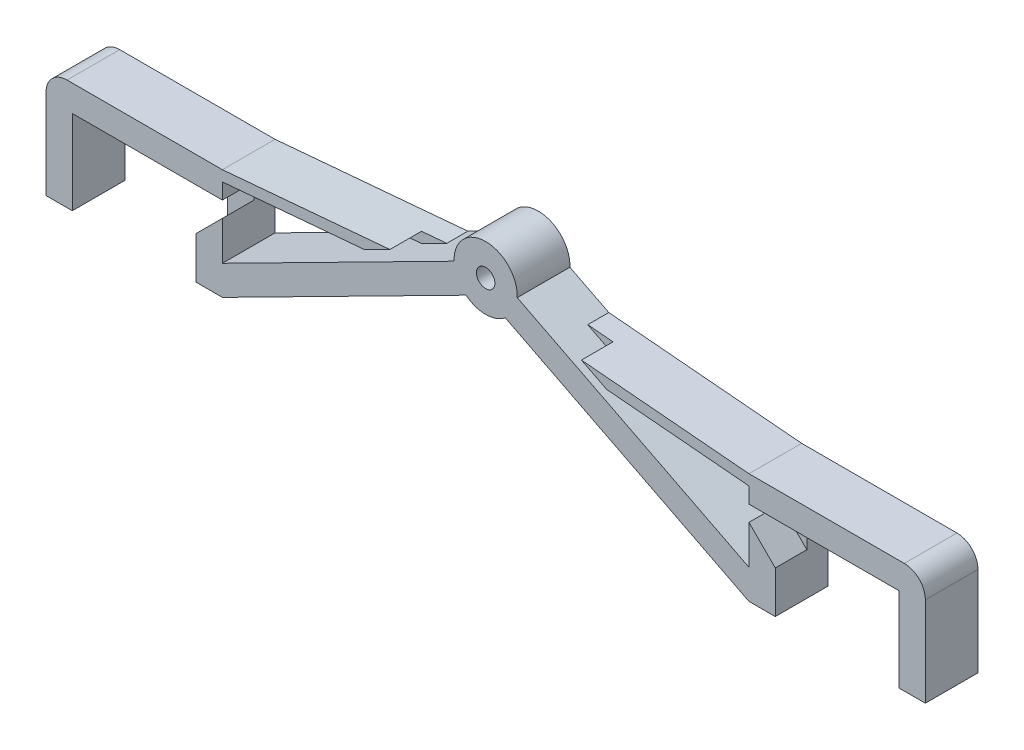
SolidWorks part; units mm, degrees
material "ABS"
ref_plane "Přední rovina" through (0, 0, 0) normal (0, 0, 1) x (1, 0, 0)
ref_plane "Horní rovina" through (0, 0, 0) normal (0, 1, 0) x (1, 0, 0)
ref_plane "Pravá rovina" through (0, 0, 0) normal (1, 0, 0) x (0, 0, -1)
sketch "Skica1" plane through (0, 0, 0) normal (0, 0, 1) x (1, 0, 0)
  line L0 (0, 0) -> (0, 16)
  line L1 (0, 16) -> (23.5, 16)
  line L2 (23.5, 16) -> (23.5, 0)
  line L3 (23.5, 0) -> (28.5, 0)
  line L4 (28.5, 0) -> (74.7688, 23.4973)
  line L5 (0, 0) -> (-5, 0)
  line L6 (-5, 0) -> (-5, 21)
  line L7 (-5, 21) -> (28.5, 21)
  line L8 (28.5, 21) -> (28.5, 5.6078)
  line L9 (28.5, 5.6078) -> (72.5048, 27.9554)
  line L10 (78.5, 31) -> (78.5, 25.3922) construction
  line L11 (78.5, 25.3922) -> (82.2312, 23.4973) construction
  line L12 (84.4952, 27.9554) -> (78.5, 31) construction
  line L13 (128.5, 5.6078) -> (84.4952, 27.9554)
  line L14 (72.5048, 27.9554) -> (78.5, 31) construction
  line L15 (78.5, 31) -> (78.5, 25.3922) construction
  line L16 (78.5, 25.3922) -> (74.7688, 23.4973) construction
  line L17 (78.5, 31) -> (78.5, 46.3264) construction
  line L18 (128.5, 21) -> (128.5, 5.6078)
  line L19 (78.5, 25.3922) -> (78.5, 12.6076) construction
  line L20 (162, 21) -> (128.5, 21)
  line L21 (162, 0) -> (162, 21)
  line L22 (157, 0) -> (162, 0)
  line L23 (128.5, 0) -> (82.2312, 23.4973)
  line L24 (133.5, 0) -> (128.5, 0)
  line L25 (133.5, 16) -> (133.5, 0)
  line L26 (157, 16) -> (133.5, 16)
  line L27 (157, 0) -> (157, 16)
  arc A0 (74.7688, 23.4973) -> (82.2312, 23.4973) centre (78.5, 28.1961) ccw
  arc A1 (84.4952, 27.9554) -> (72.5048, 27.9554) centre (78.5, 28.1961) ccw
  circle A2 centre (78.5, 28.1961) radius 1.75
  dimension "D11" = 12
  dimension "D12" = 3.5
  dimension "D1" = 5
  dimension "D2" = 5
  dimension "D3" = 23.5
  dimension "D4" = 16
  dimension "D5" = 5
  dimension "D6" = 5
  dimension "D7" = 5
  dimension "D8" = 55
  dimension "D9" = 10
extrude "Přidat vysunutím1" add sketch "Skica1" along normal mid plane 10
fillet "Zaoblit1" radius 4 2 edges at (-5, 21, 0) (162, 21, 0)
sketch "Skica2" plane through (0, 0, 0) normal (0, 0, 1) x (1, 0, 0)
  line L0 (28.5, 21) -> (65.1171, 24.2036)
  line L1 (72.5048, 27.9554) -> (28.5, 5.6078) construction
  line L2 (65.1171, 24.2036) -> (60.341, 21.7781)
  line L3 (60.341, 21.7781) -> (28.5, 18.9924)
  line L4 (28.5, 5.6078) -> (28.5, 21) construction
  line L5 (28.5, 18.9924) -> (28.5, 21)
  line L6 (28.5, 21) -> (-1, 21) construction
  dimension "D1" = 2
  dimension "D2" = 175
extrude "Přidat vysunutím2" add sketch "Skica2" along normal mid plane 10
ref_plane "Rovina1" through (78.5, 0, 0) normal (-1, 0, 0) x (0, 0, 1)
mirror "Zrcadlit1" about plane through (78.5, 0, 0) normal (-1, 0, 0) of "Přidat vysunutím2"
sketch "Skica3" plane through (0, 0, 0) normal (0, -1, 0) x (1, 0, 0)
  line L0 (11.75, -5) -> (11.75, 5) construction
  line L1 (0, -5) -> (23.5, -5) construction
  line L2 (0, 5) -> (23.5, 5) construction
  line L5 (11.75, 0) -> (-1.75, 0) construction
  line L6 (11.75, 0) -> (25.25, 0) construction
  circle A0 centre (-1.75, 0) radius 1.05
  circle A1 centre (25.25, 0) radius 1.05
  dimension "D1" = 2.1
  dimension "D2" = 27
extrude "Odebrat vysunutím1" cut sketch "Skica3" against normal blind 6
mirror "Zrcadlit2" about plane through (78.5, 0, 0) normal (-1, 0, 0) of "Odebrat vysunutím1"
sketch "Skica4" plane through (0, 0, 5) normal (0, 0, 1) x (1, 0, 0)
  line L0 (23.5, 16) -> (28.5, 16)
  line L1 (28.5, 5.6078) -> (28.5, 18.9924) construction
  line L2 (28.5, 16) -> (28.5, 13)
  line L3 (28.5, 13) -> (23.5, 8)
  line L4 (23.5, 16) -> (23.5, 0) construction
  line L5 (23.5, 8) -> (23.5, 16)
  dimension "D1" = 45
  dimension "D2" = 3
  dimension "D3" = 8
extrude "Odebrat vysunutím2" cut sketch "Skica4" against normal blind 6
mirror "Zrcadlit3" about plane through (78.5, 0, 0) normal (-1, 0, 0) of "Odebrat vysunutím2"
sketch "Skica5" plane through (0, 0, 5) normal (0, 0, 1) x (1, 0, 0)
  line L0 (60.341, 21.7781) -> (65.1171, 24.2036)
  line L1 (65.1171, 24.2036) -> (60.3145, 23.7834)
  line L2 (65.1171, 24.2036) -> (28.5, 21) construction
  line L3 (60.3145, 23.7834) -> (55.5384, 21.3579)
  line L4 (28.5, 18.9924) -> (60.341, 21.7781) construction
  line L5 (55.5384, 21.3579) -> (60.341, 21.7781)
  line L6 (91.8829, 24.2036) -> (96.6855, 23.7834)
  line L7 (91.8829, 24.2036) -> (128.5, 21) construction
  line L8 (101.4616, 21.3579) -> (96.659, 21.7781)
  line L9 (128.5, 18.9924) -> (96.659, 21.7781) construction
  line L10 (101.4616, 21.3579) -> (96.6855, 23.7834)
  line L11 (96.659, 21.7781) -> (91.8829, 24.2036)
  dimension "D1" = 1.8
  dimension "D2" = 1.8
extrude "Odebrat vysunutím3" cut sketch "Skica5" against normal up to surface (6 mm away) up to face at (26, 13.25, -1)
